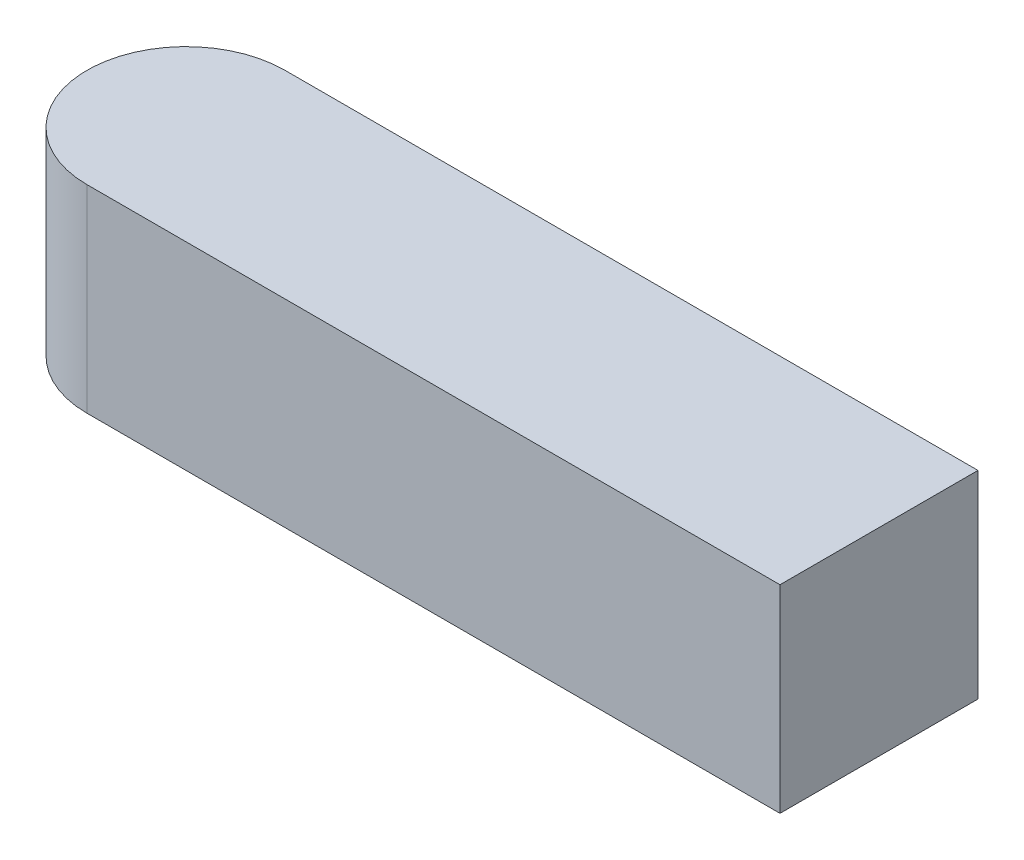
SolidWorks part; units mm, degrees
ref_plane "Front Plane" through (0, 0, 0) normal (0, 0, 1) x (1, 0, 0)
ref_plane "Top Plane" through (0, 0, 0) normal (0, 1, 0) x (1, 0, 0)
ref_plane "Right Plane" through (0, 0, 0) normal (1, 0, 0) x (0, 0, -1)
sketch "Sketch1" plane through (0, 0, 0) normal (0, 1, 0) x (1, 0, 0)
  line L0 (-80, 0) -> (80, 0) construction
  line L1 (-70, 0) -> (70, 0) construction
  line L2 (-70, 10) -> (70, 10)
  line L3 (-70, -10) -> (70, -10)
  arc A0 (-70, 10) -> (-70, -10) centre (-70, 0) ccw
  arc A1 (70, -10) -> (70, 10) centre (70, 0) ccw
  point P4 (0, 0)
  point P7 (0, 0)
  point P12 (0, 0)
  point P13 (0, 0)
  point P14 (0, 0)
  point P15 (0, 0)
  dimension "D" = 10
  dimension "L" = 160
extrude "Boss-Extrude1" add sketch "Sketch1" along normal blind 20
sketch "Sketch2" plane through (0, 20, 0) normal (0, 1, 0) x (1, 0, 0)
  line L0 (70, 10) -> (-70, 10) construction
  line L1 (0, 10) -> (80, 10)
  line L2 (0, 10) -> (0, -10)
  line L3 (0, -10) -> (80, -10)
  line L4 (80, 10) -> (80, -10)
  line L5 (-70, -10) -> (70, -10) construction
  arc A0 (70, -10) -> (70, 10) centre (70, 0) ccw construction
  point P6 (0, 0)
extrude "Cut-Extrude1" cut sketch "Sketch2" against normal through all
equation "\"L\" = 160"
equation "\"D\" = 10"
equation "\"H\"= 20"
equation "\"Cut-Extrude1\"= IIF ( \"L\" = 160 , \"unsuppressed\" , IIF ( \"L\" = 100 , \"unsuppressed\" , \"suppressed\" ) )"
equation "\"L@Sketch1\"=\"L\""
equation "\"D@Sketch1\"=\"D\""
equation "\"H@Boss-Extrude1\"=\"H\""
